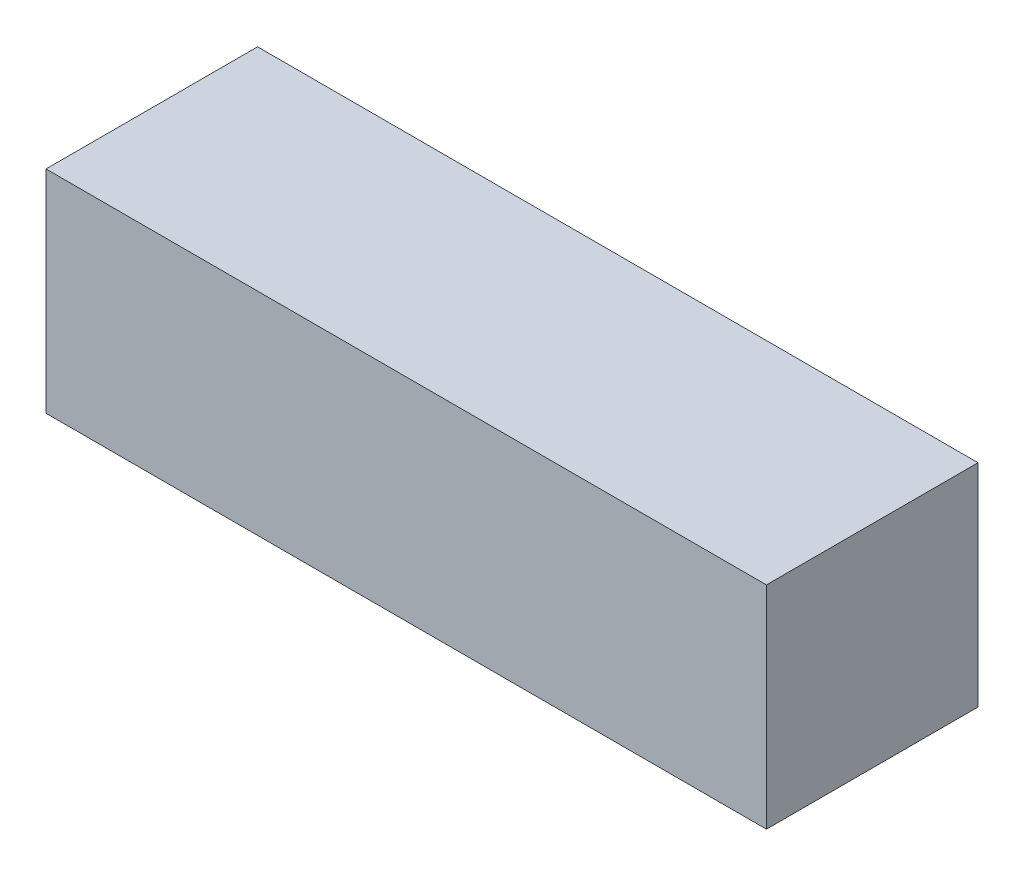
SolidWorks part; units mm, degrees
ref_plane "Front Plane" through (0, 0, 0) normal (0, 0, 1) x (1, 0, 0)
ref_plane "Top Plane" through (0, 0, 0) normal (0, 1, 0) x (1, 0, 0)
ref_plane "Right Plane" through (0, 0, 0) normal (1, 0, 0) x (0, 0, -1)
sketch "Sketch1" plane through (0, 0, 0) normal (0, 1, 0) x (1, 0, 0)
  line L1 (-170.25, -50) -> (170.25, -50)
  line L2 (-170.25, -50) -> (-170.25, 50)
  line L3 (-170.25, 50) -> (170.25, 50)
  line L4 (170.25, -50) -> (170.25, 50)
  line L5 (-170.25, -50) -> (170.25, 50) construction
  line L6 (-170.25, 50) -> (170.25, -50) construction
  point P0 (0, 0)
extrude "Boss-Extrude1" add sketch "Sketch1" along normal blind 100
sketch "Sketch2" plane through (0, 100, 0) normal (0, 1, 0) x (1, 0, 0)
  text T0 "3U CUBESAT" font "Century Gothic" height 3.175
